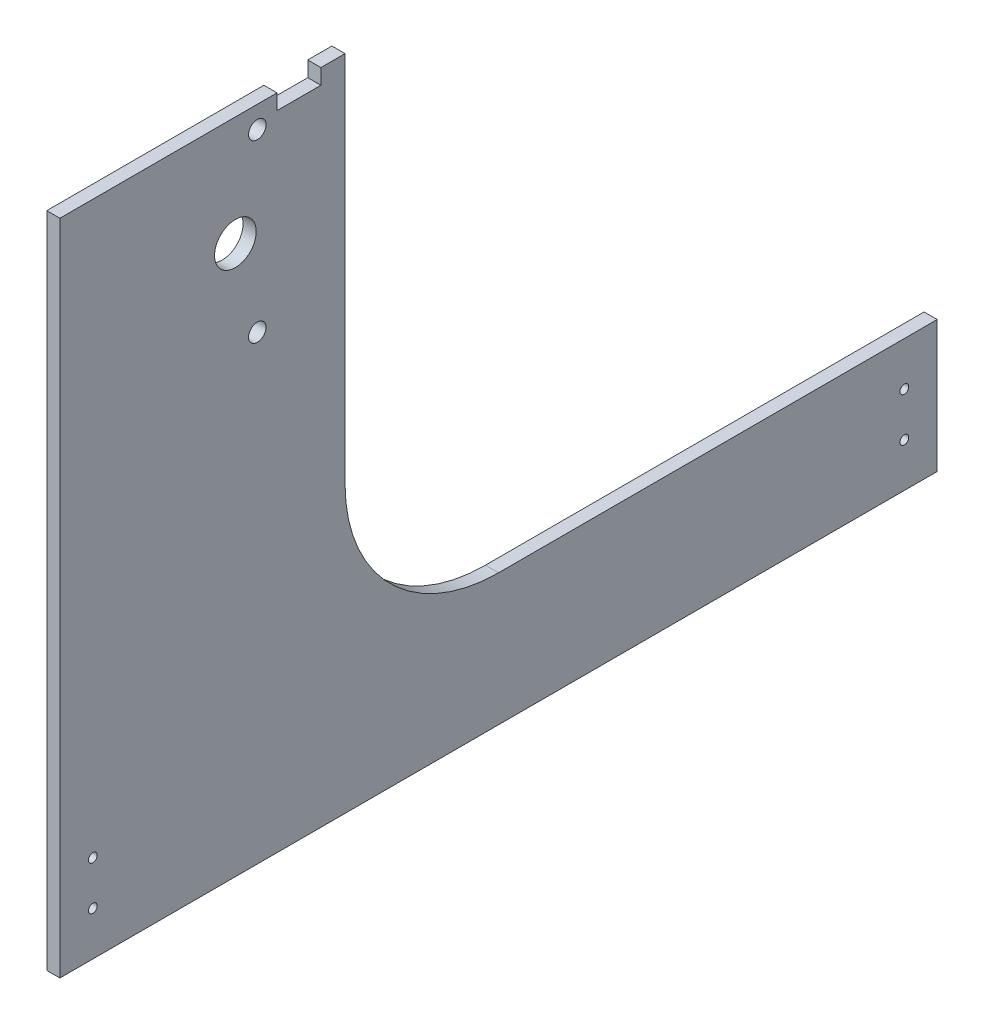
SolidWorks part; units mm, degrees
material "Acrylic (Medium-high impact)"
ref_plane "Front Plane" through (0, 0, 0) normal (0, 0, 1) x (1, 0, 0)
ref_plane "Top Plane" through (0, 0, 0) normal (0, 1, 0) x (1, 0, 0)
ref_plane "Right Plane" through (0, 0, 0) normal (1, 0, 0) x (0, 0, -1)
sketch "Sketch1" plane through (0, 0, 0) normal (1, 0, 0) x (0, 0, -1)
  line L0 (-1000, 0) -> (49000, 0) construction
  line L1 (-80, -250) -> (320, -250)
  line L6 (-900, -190) -> (49100, -190) construction
  line L7 (0, -1000) -> (0, 49000) construction
  line L10 (-80, -190) -> (-80, -250)
  line L11 (-30, 50) -> (-30, -120.0496)
  line L12 (84.8849, -120.0496) -> (-119.1387, -120.0496) construction
  line L20 (0, -750) -> (0, 49250) construction
  line L30 (320, -190) -> (320, -250)
  line L31 (50, 50) -> (50, -120)
  line L32 (-30, 50) -> (50, 50)
  line L33 (120, -190) -> (320, -190)
  line L34 (-27.1942, 0) -> (27.1942, 0) construction
  line L39 (10, -950) -> (10, 49050) construction
  line L40 (39, 50) -> (19, 50)
  line L41 (39, 50) -> (39, 43)
  line L42 (39, 43) -> (19, 43)
  line L43 (19, 50) -> (19, 43)
  circle A1 centre (0, 0) radius 4
  circle A2 centre (10, -40) radius 4
  circle A3 centre (10, 40) radius 4
  arc A5 (120, -190) -> (50, -120) centre (120, -120) cw
  arc A8 (-80, -190) -> (-30, -120.0496) centre (-103.9305, -120.0496) ccw
  point P0 (0, 0)
  point P51 (0, 0)
  dimension "D7" = 73.9305
  dimension "D14" = 8
  dimension "D16" = 40
  dimension "D18" = 120
  dimension "D12" = 70
  dimension "D13" = 7
  dimension "D20" = 9
  dimension "D6" = 10
  dimension "D2" = 400
  dimension "D3" = 50
  dimension "D4" = 30
  dimension "D5" = 250
  dimension "D8" = 300
  dimension "D9" = 70
  dimension "D11" = 60
  dimension "D10" = 50
  dimension "D15" = 50
  dimension "D17" = 40
  dimension "D19" = 20
extrude "Boss-Extrude1" add sketch "Sketch1" along normal blind 6
sketch "Sketch3" plane through (6, 0, 0) normal (1, 0, 0) x (0, 0, -1)
  circle A0 centre (0, 0) radius 9.5
  dimension "D1" = 19
extrude "Cut-Extrude1" cut sketch "Sketch3" against normal up to next
sketch "Sketch4" plane through (0, 0, 0) normal (-1, 0, 0) x (0, 0, 1)
  line L1 (80, -250) -> (30, -250)
  line L2 (80, -250) -> (80, 50)
  line L3 (80, 50) -> (30, 50)
  line L4 (30, -250) -> (30, 50)
extrude "Boss-Extrude2" add sketch "Sketch4" against normal blind 6
sketch "Sketch5" plane through (0, 0, 0) normal (-1, 0, 0) x (0, 0, 1)
  line L0 (80, -250) -> (-320, -250) construction
  line L1 (80, 50) -> (80, -250) construction
  line L2 (-120, -1250) -> (-120, 48750) construction
  circle A0 centre (65, -210) radius 2
  circle A1 centre (65, -230) radius 2
  circle A2 centre (-305, -230) radius 2
  circle A3 centre (-305, -210) radius 2
  point P11 (-120, -250)
  dimension "D1" = 4
  dimension "D2" = 20
  dimension "D4" = 15
  dimension "D5" = 15
  dimension "D3" = 20
extrude "Cut-Extrude2" cut sketch "Sketch5" against normal up to next
